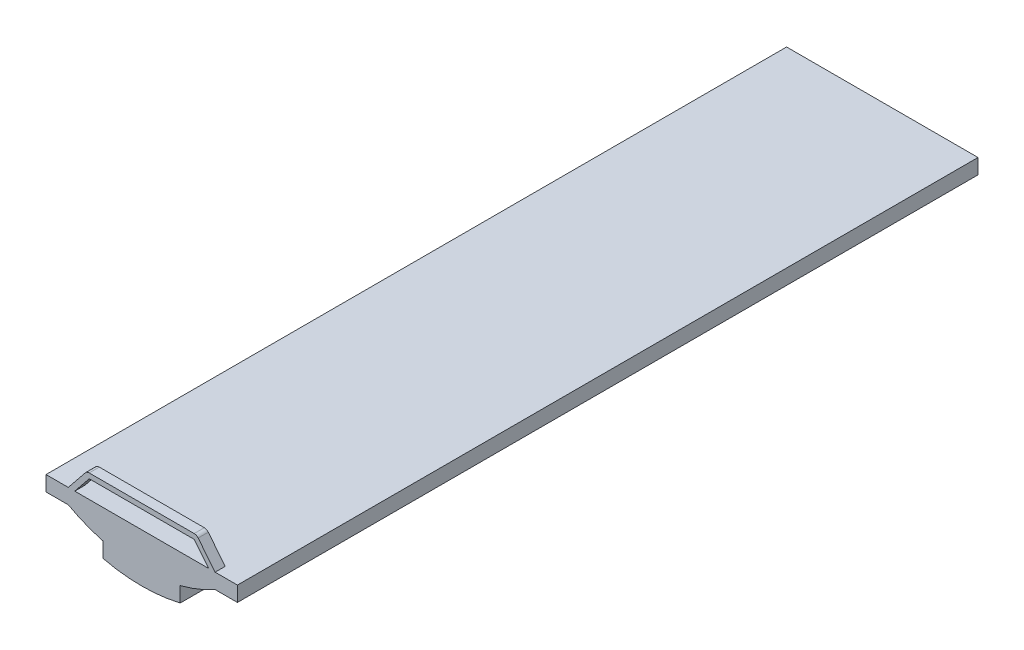
SolidWorks part; units mm, degrees
ref_plane "Front Plane" through (0, 0, 0) normal (0, 0, 1) x (1, 0, 0)
ref_plane "Top Plane" through (0, 0, 0) normal (0, 1, 0) x (1, 0, 0)
ref_plane "Right Plane" through (0, 0, 0) normal (1, 0, 0) x (0, 0, -1)
sketch "Sketch1" plane through (0, 0, 0) normal (0, 0, 1) x (1, 0, 0)
  line L0 (0, 0) -> (0, -4.4806)
  line L1 (0, -4.4806) -> (6.6209, -4.4806)
  line L2 (16.9859, -8.6396) -> (16.9859, -13.1203)
  line L3 (39.8773, -8.6396) -> (39.8773, -13.1203)
  line L4 (56.8632, 0) -> (56.8632, -4.4806)
  line L5 (56.8632, -4.4806) -> (50.2423, -4.4806)
  line L6 (0, 0) -> (56.8632, 0)
  arc A0 (6.6209, -4.4806) -> (16.9859, -8.6396) centre (28.4316, 34.8804) ccw
  arc A1 (16.9859, -13.1203) -> (39.8773, -13.1203) centre (28.4316, 34.8804) ccw
  arc A2 (39.8773, -8.6396) -> (50.2423, -4.4806) centre (28.4316, 34.8804) ccw
extrude "Boss-Extrude1" add sketch "Sketch1" along normal blind 220
sketch "Sketch2" plane through (0, 0, 220) normal (0, 0, 1) x (1, 0, 0)
  line L0 (6.6209, 0) -> (12.1134, 6.8325)
  line L1 (56.8632, 0) -> (0, 0) construction
  line L2 (12.1134, 6.8325) -> (44.7498, 6.8325)
  line L3 (50.2423, 0) -> (44.7498, 6.8325)
  line L4 (8.5455, 0) -> (12.8321, 5.3325)
  line L5 (12.8321, 5.3325) -> (44.0311, 5.3325)
  line L6 (48.3177, 0) -> (44.0311, 5.3325)
  line L7 (6.6209, 0) -> (8.5455, 0)
  line L8 (50.2423, 0) -> (48.3177, 0)
  line L10 (7.79, -0.9398) -> (12.8321, 5.3325) construction
  line L11 (49.0732, -0.9398) -> (44.0311, 5.3325) construction
  dimension "D1" = 1.5
extrude "Boss-Extrude2" add sketch "Sketch2" against normal blind 3
fillet "Fillet1" radius 1.5 2 edges at (12.1134, 6.8325, 218.5) (44.7498, 6.8325, 218.5)
scale "Scale1" scale about centroid uniform scaling yes scale factor 15.6
scale "Scale2" scale about centroid uniform scaling yes scale factor 0.5
